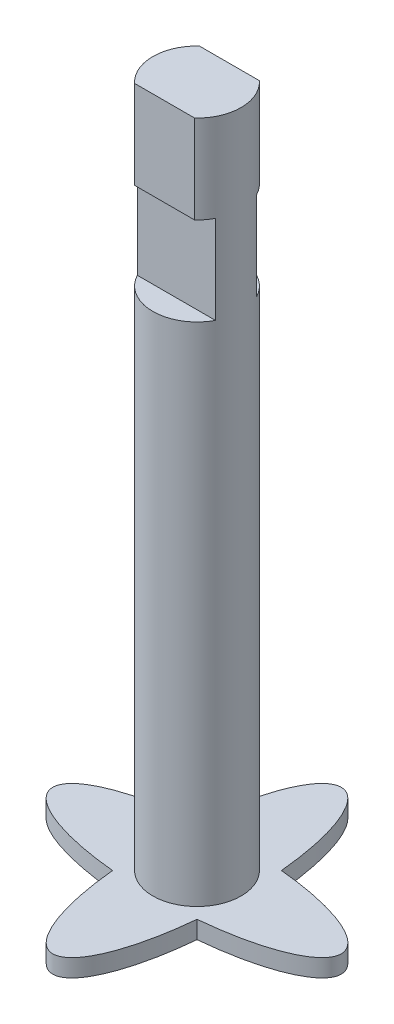
SolidWorks part; units mm, degrees
ref_plane "Front Plane" through (0, 0, 0) normal (0, 0, 1) x (1, 0, 0)
ref_plane "Top Plane" through (0, 0, 0) normal (0, 1, 0) x (1, 0, 0)
ref_plane "Right Plane" through (0, 0, 0) normal (1, 0, 0) x (0, 0, -1)
sketch "Sketch1" plane through (0, 0, 0) normal (0, 1, 0) x (1, 0, 0)
  circle A0 centre (0, 0) radius 3.75 construction
  ellipse E0 centre (0, 0) end of major axis (12.25, 0) minor radius 3.75
  ellipse E1 centre (0, 0) end of major axis (0, 12.25) minor radius 3.75
  dimension "D1" = 7.5
  dimension "D2" = 24.5
  dimension "D3" = 24.5
extrude "Boss-Extrude1" add sketch "Sketch1" along normal blind 1.5
sketch "Sketch2" plane through (0, 1.5, 0) normal (0, 1, 0) x (1, 0, 0)
  circle A0 centre (0, 0) radius 3.75
  dimension "D1" = 7.5
extrude "Boss-Extrude2" add sketch "Sketch2" along normal blind 58
ref_plane "Plane1" through (0, 0, 3.75) normal (0, 0, 1) x (1, 0, 0)
sketch "Sketch3" plane through (0, 0, 3.75) normal (0, 0, 1) x (1, 0, 0)
  line L0 (0, 59.5) -> (0, -5.4703) construction
  line L1 (-3.75, 59.5) -> (3.75, 59.5)
  line L2 (-3.75, 59.5) -> (-3.75, 44.5)
  line L3 (-3.75, 44.5) -> (3.75, 44.5)
  line L4 (3.75, 59.5) -> (3.75, 44.5)
  line L5 (3.75, 59.5) -> (-3.75, 59.5) construction
  dimension "D1" = 7.5
  dimension "D2" = 15
extrude "Cut-Extrude1" cut sketch "Sketch3" against normal blind 1
sketch "Sketch4" plane through (0, 0, 2.75) normal (0, 0, 1) x (1, 0, 0)
  line L1 (-6.098, 44.5) -> (6.3936, 44.5)
  line L2 (-6.098, 44.5) -> (-6.098, 52)
  line L3 (-6.098, 52) -> (6.3936, 52)
  line L4 (6.3936, 44.5) -> (6.3936, 52)
  point P7 (-2.5495, 52)
extrude "Cut-Extrude2" cut sketch "Sketch4" against normal blind 1
pattern_circular "CirPattern1" count 2 over 360 about axis through (0, 59.5, 0) along (0, 1, 0) of "Cut-Extrude1", "Cut-Extrude2"
